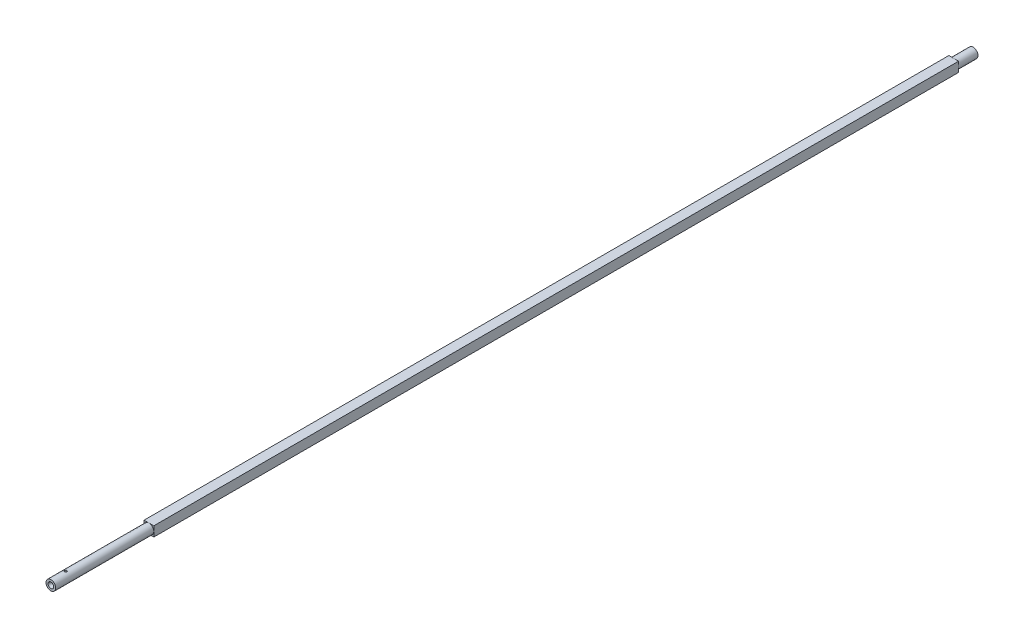
SolidWorks part; units mm, degrees
material "1060 Alloy"
ref_plane "Front Plane" through (0, 0, 0) normal (0, 0, 1) x (1, 0, 0)
ref_plane "Top Plane" through (0, 0, 0) normal (0, 1, 0) x (1, 0, 0)
ref_plane "Right Plane" through (0, 0, 0) normal (1, 0, 0) x (0, 0, -1)
sketch "Sketch1" plane through (0, 0, 0) normal (1, 0, 0) x (0, 0, -1)
  line L0 (0, 0) -> (-3.0596, 0) construction
  line L1 (5, 0) -> (592.2, 0)
  line L2 (0, 1.805) -> (0, 3.155)
  line L3 (0, 3.155) -> (597.2, 3.155)
  line L4 (597.2, 1.805) -> (597.2, 3.155)
  line L5 (0, 1.805) -> (5, 0)
  line L6 (597.2, 1.805) -> (592.2, 0)
  line L7 (0, 0) -> (0, 1.805) construction
  line L8 (0, 0) -> (5, 0) construction
  line L9 (592.2, 0) -> (597.2, 0) construction
  line L10 (597.2, 0) -> (597.2, 1.805) construction
  dimension "D1" = 6.31
  dimension "D2" = 5
  dimension "D3" = 3.61
  dimension "D4" = 597.2
revolve "Revolve1" add sketch "Sketch1" angle 360 about L0
ref_plane "Plane1" through (0, 0, -63.5) normal (0, 0, 1) x (1, 0, 0)
ref_plane "Plane2" through (0, 0, -584.64) normal (0, 0, -1) x (-1, 0, 0)
sketch "Sketch2" plane through (0, 0, -63.5) normal (0, 0, 1) x (1, 0, 0)
  line L0 (0, 0) -> (0, 8.8287) construction
  line L1 (-3.16, 3.16) -> (3.16, 3.16)
  line L2 (-3.16, 3.16) -> (-3.16, -3.16)
  line L3 (-3.16, -3.16) -> (3.16, -3.16)
  line L4 (3.16, 3.16) -> (3.16, -3.16)
  line L5 (0, 0) -> (13.7494, 0) construction
  dimension "D1" = 6.32
extrude "Boss-Extrude1" add sketch "Sketch2" against normal up to surface (521.14 mm away) up to plane "Plane2"
sketch "Sketch4" plane through (0, 0, 0) normal (0, 1, 0) x (1, 0, 0)
  line L0 (0, 0) -> (0, 9.525) construction
  line L1 (0, 8.75) -> (4.3679, 8.75) construction
  circle A0 centre (0, 9.525) radius 0.775
  dimension "D2" = 1.55
  dimension "D1" = 8.75
extrude "Cut-Extrude1" cut sketch "Sketch4" against normal through all and the other way through all
